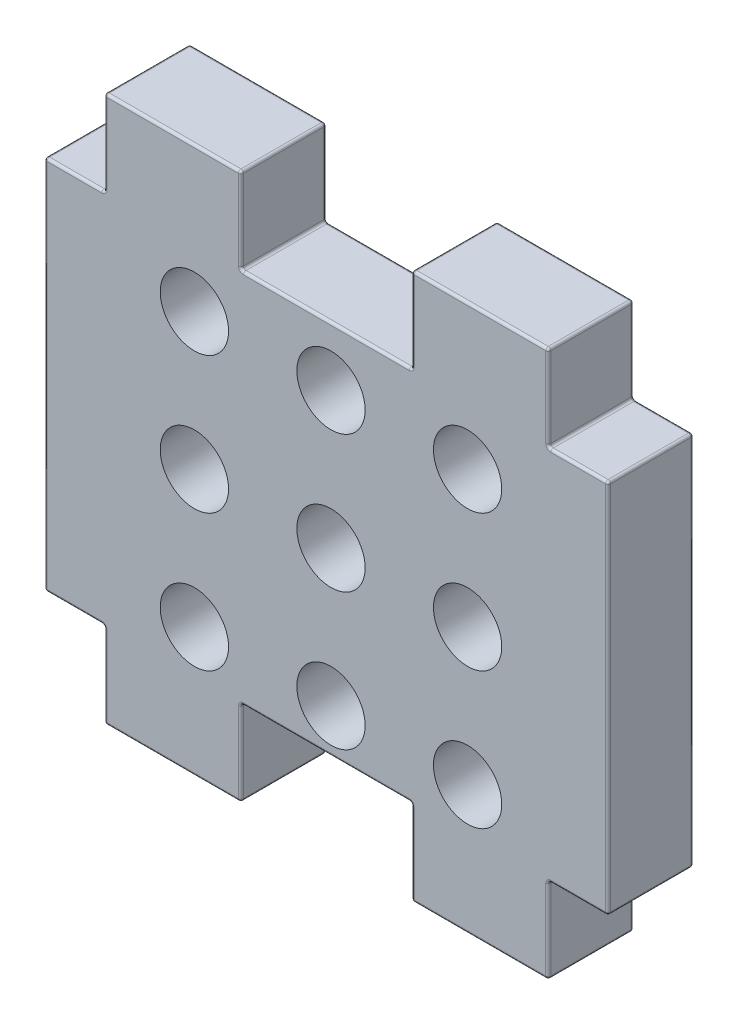
SolidWorks part; units mm, degrees
ref_plane "Płaszczyzna przednia" through (0, 0, 0) normal (0, 0, 1) x (1, 0, 0)
ref_plane "Płaszczyzna górna" through (0, 0, 0) normal (0, 1, 0) x (1, 0, 0)
ref_plane "Płaszczyzna prawa" through (0, 0, 0) normal (1, 0, 0) x (0, 0, -1)
sketch "Szkic1" plane through (0, 0, 0) normal (0, 0, 1) x (1, 0, 0)
  line L0 (-16.5, 11) -> (16.5, 11)
  line L7 (16.5, -11) -> (16.5, 11)
  line L8 (-16.5, -11) -> (16.5, -11)
  line L9 (-16.5, -11) -> (-16.5, 11)
  line L10 (-13, 11) -> (-13, 16)
  line L11 (-13, 16) -> (-5, 16)
  line L12 (-5, 16) -> (-5, 11)
  line L14 (-11.5, 0) -> (-13, 0) construction
  line L15 (5, 16) -> (5, 11)
  line L16 (13, 16) -> (5, 16)
  line L17 (13, 11) -> (13, 16)
  line L18 (13, -11) -> (13, -16)
  line L19 (13, -16) -> (5, -16)
  line L20 (5, -16) -> (5, -11)
  line L21 (-13, -11) -> (-13, -16)
  line L22 (-13, -16) -> (-5, -16)
  line L23 (-5, -16) -> (-5, -11)
  line L26 (-15, 0) -> (-16.5, 0) construction
  circle A0 centre (8.274, 7.5559) radius 2
  circle A1 centre (-7.726, -8.4441) radius 2
  circle A2 centre (-7.726, -0.4441) radius 2
  circle A3 centre (0.274, 7.5559) radius 2
  circle A4 centre (0.274, -0.4441) radius 2
  circle A5 centre (0.274, -8.4441) radius 2
  circle A6 centre (-7.726, 7.5559) radius 2
  circle A7 centre (8.274, -0.4441) radius 2
  circle A8 centre (8.274, -8.4441) radius 2
  point P0 (0, 0)
  point P1 (0, 0)
  point P2 (0, 0)
  dimension "D4" = 3.5
  dimension "D5" = 5
  dimension "D6" = 8
extrude "Dodanie-wyciągnięcie1" add sketch "Szkic1" along normal mid plane 5
fillet "Zaokrąglenie1" radius 0.15 60 edges at (-16.5, 11, 0) (-16.5, 0, -2.5) (-16.5, 0, 2.5) (-14.75, 11, 2.5) (-14.75, 11, -2.5) (-16.5, -11, 0) (-13, 11, 0) (-14.75, -11, 2.5) (-14.75, -11, -2.5) (-13, 13.5, -2.5) (-13, 13.5, 2.5) (-13, -11, 0) (-13, 16, 0) (-13, -13.5, -2.5) (-13, -13.5, 2.5) (-9, 16, -2.5) (-9, 16, 2.5) (-13, -16, 0) (-5, 16, 0) (-9, -16, -2.5) (-9, -16, 2.5) (-5, 13.5, -2.5) (-5, 13.5, 2.5) (-5, -16, 0) (-5, 11, 0) (-5, -13.5, -2.5) (-5, -13.5, 2.5) (0, 11, 2.5) (0, 11, -2.5) (-5, -11, 0) (5, 11, 0) (0, -11, 2.5) (0, -11, -2.5) (5, 13.5, -2.5) (5, 13.5, 2.5) (5, -11, 0) (5, 16, 0) (5, -13.5, -2.5) (5, -13.5, 2.5) (9, 16, -2.5) (9, 16, 2.5) (5, -16, 0) (13, 16, 0) (9, -16, -2.5) (9, -16, 2.5) (13, 13.5, -2.5) (13, 13.5, 2.5) (13, -16, 0) (13, 11, 0) (13, -13.5, -2.5) (13, -13.5, 2.5) (14.75, 11, 2.5) (14.75, 11, -2.5) (13, -11, 0) (16.5, 11, 0) (14.75, -11, 2.5) (14.75, -11, -2.5) (16.5, 0, -2.5) (16.5, 0, 2.5) (16.5, -11, 0)
